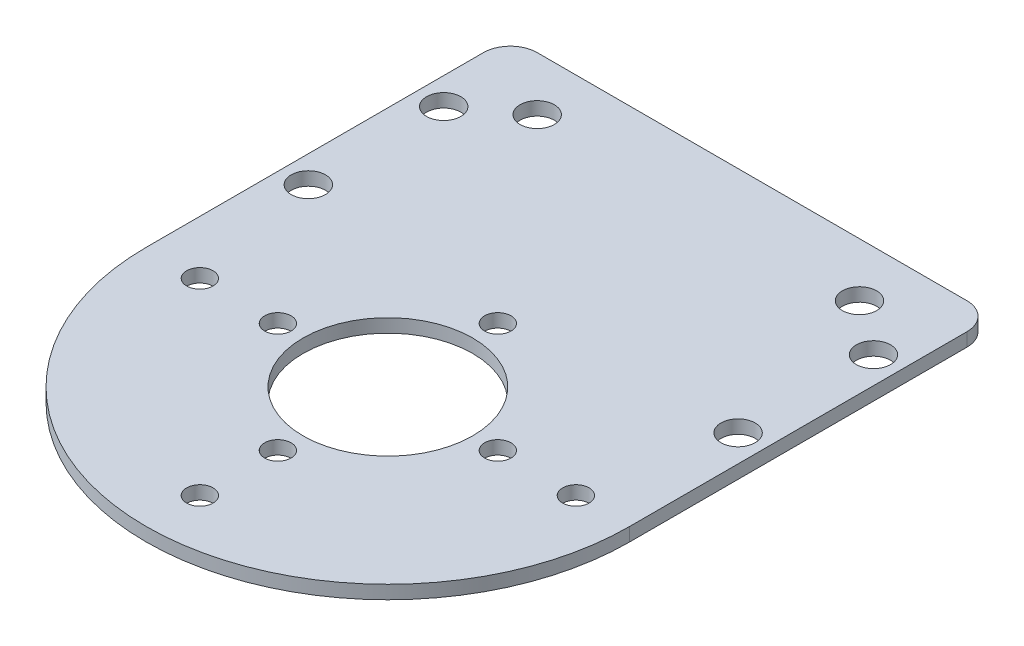
SolidWorks part; units mm, degrees
ref_plane "Front Plane" through (0, 0, 0) normal (0, 0, 1) x (1, 0, 0)
ref_plane "Top Plane" through (0, 0, 0) normal (0, 1, 0) x (1, 0, 0)
ref_plane "Right Plane" through (0, 0, 0) normal (1, 0, 0) x (0, 0, -1)
sketch "Sketch1" plane through (0, 0, 0) normal (0, 1, 0) x (1, 0, 0)
  line L0 (-28.575, 0) -> (-28.575, 39.875)
  line L1 (-25.4, 43.05) -> (25.4, 43.05)
  line L2 (28.575, 39.875) -> (28.575, 0)
  line L3 (0, 0) -> (0, 24) construction
  line L4 (-28.575, 31.75) -> (28.575, 31.75) construction
  line L5 (-25.4, 32) -> (25.4, 16) construction
  circle A0 centre (0, 0) radius 10.025
  circle A1 centre (0, 0) radius 13 construction
  circle A2 centre (0, -13) radius 1.5625
  circle A3 centre (-13, 0) radius 1.5625
  circle A4 centre (0, 13) radius 1.5625
  circle A5 centre (13, 0) radius 1.5625
  arc A6 (-28.575, 0) -> (28.575, 0) centre (0, 0) ccw
  circle A7 centre (0, 0) radius 20 construction
  circle A8 centre (0, 0) radius 22.225 construction
  circle A9 centre (-22.225, 0) radius 1.5625
  circle A10 centre (0, -22.225) radius 1.5625
  circle A11 centre (22.225, 0) radius 1.5625
  circle A12 centre (-25.4, 16) radius 2.025
  circle A13 centre (25.4, 16) radius 2.025
  circle A14 centre (25.4, 32) radius 2.025
  circle A15 centre (-25.4, 32) radius 2.025
  circle A16 centre (-19.05, 36.7) radius 2.025
  circle A17 centre (19.05, 36.7) radius 2.025
  arc A18 (25.4, 43.05) -> (28.575, 39.875) centre (25.4, 39.875) cw
  arc A19 (-28.575, 39.875) -> (-25.4, 43.05) centre (-25.4, 39.875) cw
  circle A20 centre (-25.4, 32) radius 3.8 construction
  point P15 (0, 0)
  point P24 (0, 0)
  point P30 (0, 22.225)
  dimension "D1" = 20.05
  dimension "D2" = 3.125
  dimension "D3" = 26
  dimension "D5" = 57.15
  dimension "D6" = 40
  dimension "D7" = 44.45
  dimension "D11" = 4.05
  dimension "D19" = 3.175
  dimension "D20" = 7.6
  dimension "D9" = 24
  dimension "D10" = 9.525
  dimension "D14" = 25.4
  dimension "D15" = 16
  dimension "D16" = 12.7
  dimension "D17" = 19.05
  dimension "D18" = 6.35
  dimension "D12" = 2
  dimension "D13" = 2
  dimension "D4" = 4
  dimension "D8" = 3
extrude "Boss-Extrude1" add sketch "Sketch1" along normal blind 1.5875
